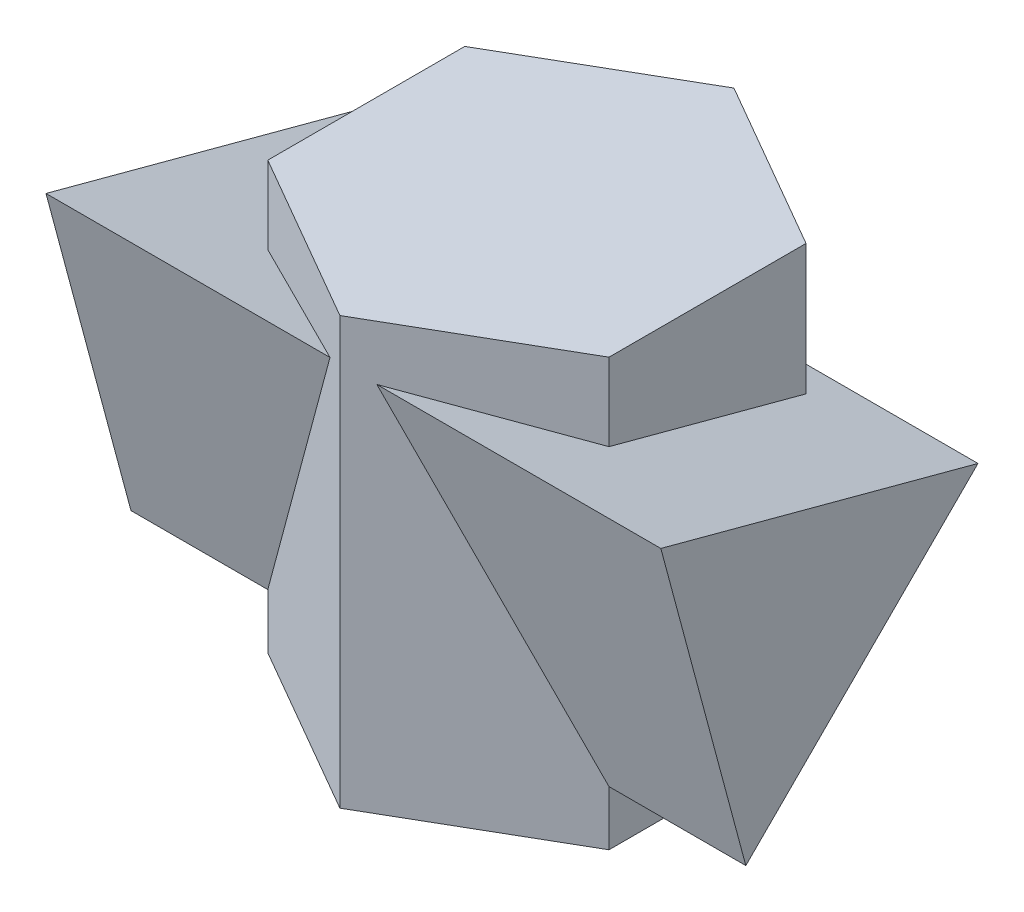
SolidWorks part; units mm, degrees
ref_plane "Front" through (0, 0, 0) normal (0, 0, 1) x (1, 0, 0)
ref_plane "Top" through (0, 0, 0) normal (0, 1, 0) x (1, 0, 0)
ref_plane "Right" through (0, 0, 0) normal (1, 0, 0) x (0, 0, -1)
sketch "Sketch2" plane through (0, 0, 0) normal (1, 0, 0) x (0, 0, -1)
  line L0 (0, 10) -> (42.4264, 52.4264)
  line L1 (42.4264, 52.4264) -> (-15.5291, 67.9555)
  line L2 (-15.5291, 67.9555) -> (0, 10)
  line L3 (0, 10) -> (25.4445, 10) construction
  dimension "D1" = 10
  dimension "D2" = 60
  dimension "D3" = 60
  dimension "D4" = 60
  dimension "D5" = 45
sketch "Sketch3" plane through (0, 0, 0) normal (0, 1, 0) x (1, 0, 0)
  line L0 (-31.1769, 0) -> (31.1769, 0) construction
  line L1 (0, 54) -> (-31.1769, 36)
  line L2 (-31.1769, 36) -> (-31.1769, 0)
  line L3 (-31.1769, 0) -> (0, -18)
  line L4 (0, -18) -> (31.1769, 0)
  line L5 (31.1769, 0) -> (31.1769, 36)
  line L6 (31.1769, 36) -> (0, 54)
  circle A0 centre (0, 18) radius 31.1769 construction
  dimension "D1" = 36
extrude "Extrude1" add sketch "Sketch3" along normal blind 77.96
extrude "Extrude2" add sketch "Sketch2" along normal mid plane 112.35
